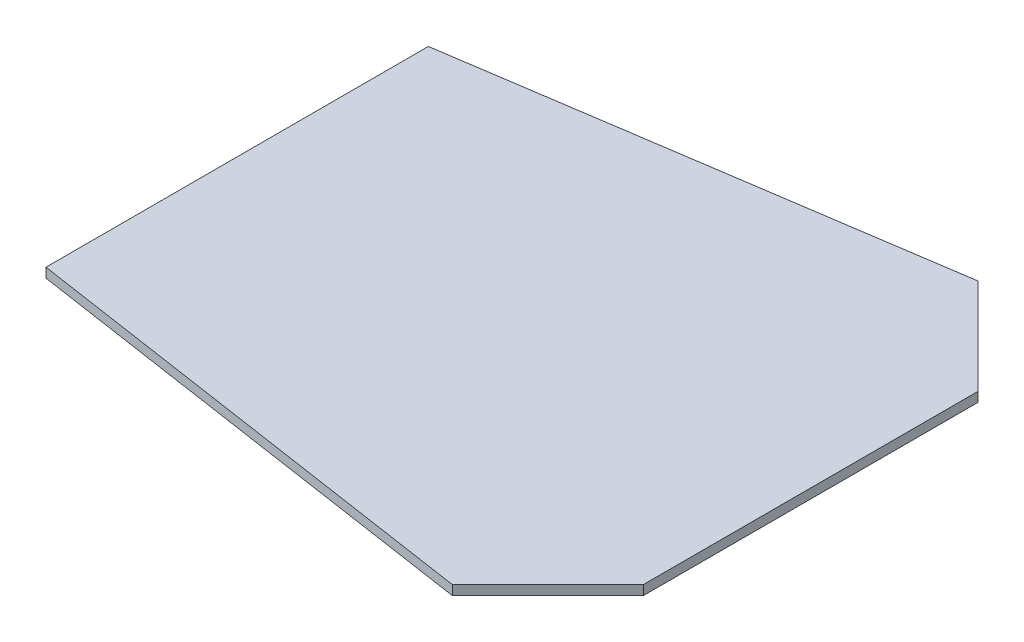
SolidWorks part; units mm, degrees
ref_plane "Front Plane" through (0, 0, 0) normal (0, 0, 1) x (1, 0, 0)
ref_plane "Top Plane" through (0, 0, 0) normal (0, 1, 0) x (1, 0, 0)
ref_plane "Right Plane" through (0, 0, 0) normal (1, 0, 0) x (0, 0, -1)
sketch "Sketch1" plane through (0, 0, 0) normal (0, 1, 0) x (1, 0, 0)
  line L0 (0, 0) -> (600, 0) construction
  line L1 (0, 200) -> (0, -200)
  line L2 (600, 175) -> (600, -175)
  line L3 (600, 175) -> (500, 275)
  line L4 (500, 275) -> (0, 200)
  line L5 (600, -175) -> (500, -275)
  line L6 (500, -275) -> (0, -200)
  point P7 (0, 0)
  point P8 (600, 0)
  dimension "D1" = 400
  dimension "D2" = 350
  dimension "D3" = 600
  dimension "D4" = 100
  dimension "D5" = 75
extrude "Boss-Extrude1" add sketch "Sketch1" along normal mid plane 10
